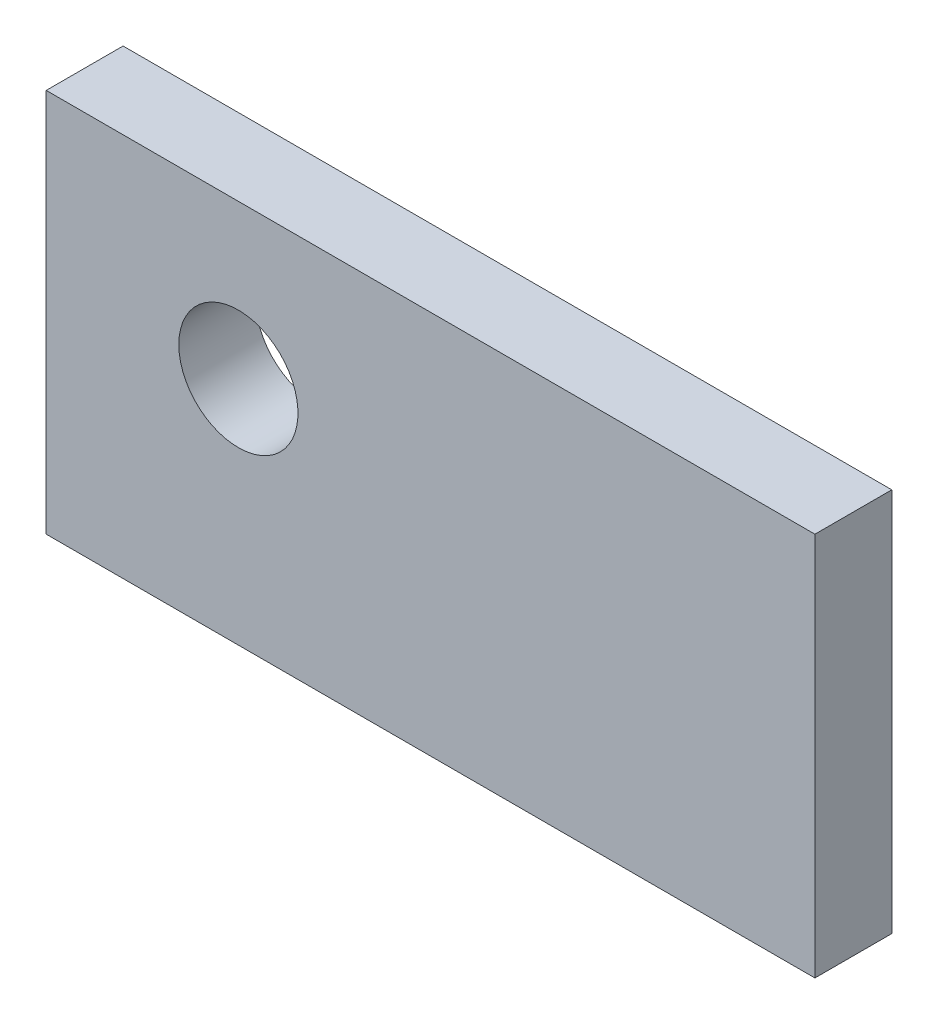
SolidWorks part; units mm, degrees
ref_plane "Спереди" through (0, 0, 0) normal (0, 0, 1) x (1, 0, 0)
ref_plane "Сверху" through (0, 0, 0) normal (0, 1, 0) x (1, 0, 0)
ref_plane "Справа" through (0, 0, 0) normal (1, 0, 0) x (0, 0, -1)
sketch "Эскиз1" plane through (0, 0, 0) normal (1, 0, 0) x (0, 0, -1)
  line L1 (0, 0) -> (4, 0)
  line L2 (0, 0) -> (0, 20)
  line L3 (0, 20) -> (4, 20)
  line L4 (4, 0) -> (4, 20)
extrude "Бобышка-Вытянуть1" add sketch "Эскиз1" along normal blind 40
sketch "Эскиз2" plane through (0, 0, -4) normal (0, 0, -1) x (-1, 0, 0)
  circle A0 centre (-10, 12) radius 3.1
extrude "Вырез-Вытянуть1" cut sketch "Эскиз2" against normal through all
